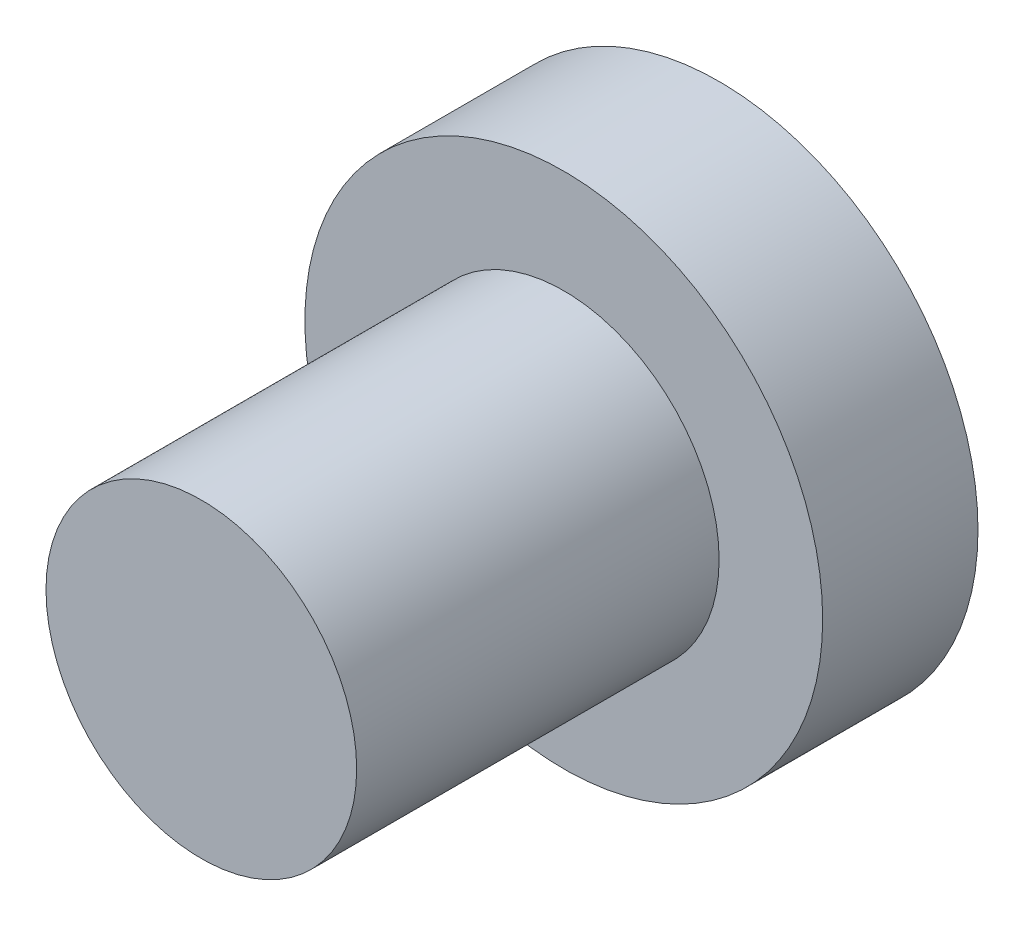
SolidWorks part; units mm, degrees
ref_plane "Front Plane" through (0, 0, 0) normal (0, 0, 1) x (1, 0, 0)
ref_plane "Top Plane" through (0, 0, 0) normal (0, 1, 0) x (1, 0, 0)
ref_plane "Right Plane" through (0, 0, 0) normal (1, 0, 0) x (0, 0, -1)
sketch "Sketch1" plane through (0, 0, 0) normal (0, 0, 1) x (1, 0, 0)
  circle A0 centre (0, 0) radius 5
  dimension "D1" = 10
extrude "Boss-Extrude1" add sketch "Sketch1" along normal blind 3
sketch "Sketch2" plane through (0, 0, 3) normal (0, 0, 1) x (1, 0, 0)
  circle A0 centre (0, 0) radius 3
extrude "Boss-Extrude2" add sketch "Sketch2" along normal blind 7
